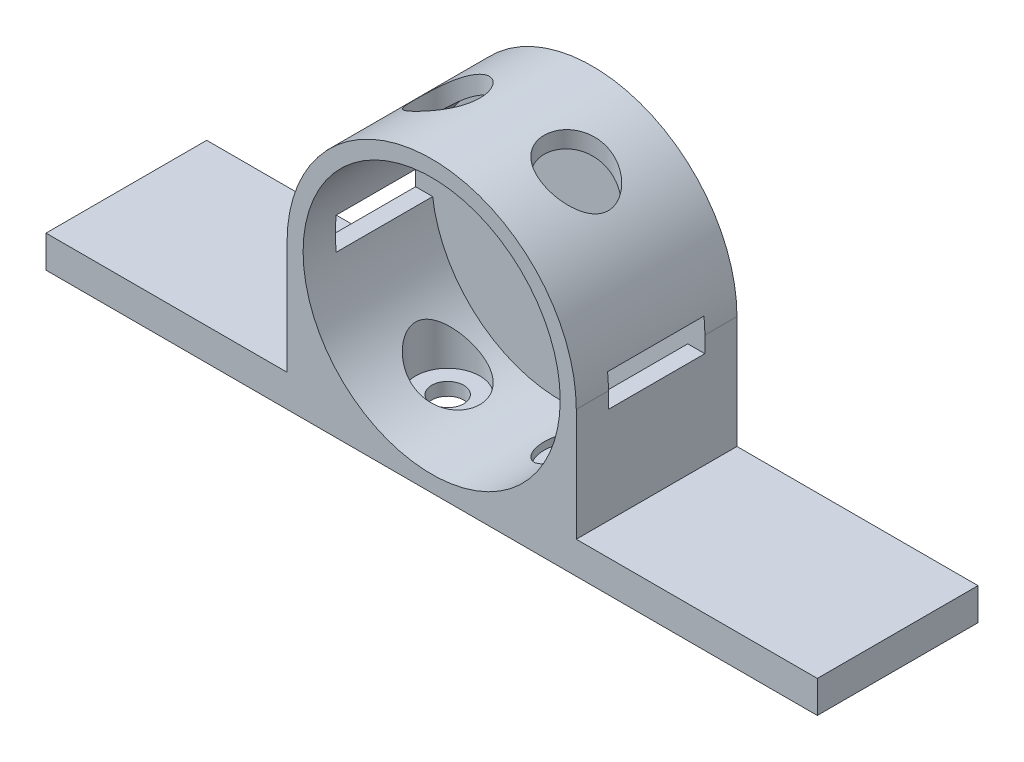
SolidWorks part; units mm, degrees
ref_plane "Front Plane" through (0, 0, 0) normal (0, 0, 1) x (1, 0, 0)
ref_plane "Top Plane" through (0, 0, 0) normal (0, 1, 0) x (1, 0, 0)
ref_plane "Right Plane" through (0, 0, 0) normal (1, 0, 0) x (0, 0, -1)
sketch "Sketch2" plane through (0, 0, 0) normal (0, 0, 1) x (1, 0, 0)
  circle A1 centre (0, 0) radius 22.5
  dimension "D2" = 45
extrude "Boss-Extrude3" add sketch "Sketch2" along normal blind 25
sketch "Sketch6" plane through (0, 0, 0) normal (0, 0, 1) x (1, 0, 0)
  line L1 (-22.5, 0) -> (22.5, 0)
  line L2 (-22.5, 0) -> (-22.5, -22.5)
  line L3 (-22.5, -22.5) -> (22.5, -22.5)
  line L4 (22.5, 0) -> (22.5, -22.5)
  circle A0 centre (0, 0) radius 22.5 construction
extrude "Boss-Extrude4" add sketch "Sketch6" along normal blind 25
sketch "Sketch4" plane through (0, 0, 25) normal (0, 0, 1) x (1, 0, 0)
  circle A0 centre (0, 0) radius 20
  dimension "D1" = 40
extrude "Cut-Extrude1" cut sketch "Sketch4" against normal blind 20
sketch "Sketch5" plane through (0, 0, 0) normal (0, 0, -1) x (-1, 0, 0)
  circle A0 centre (0, 0) radius 2.5
  dimension "D1" = 5
extrude "Cut-Extrude2" cut sketch "Sketch5" against normal up to surface (5 mm away) up to face at (20, 0, 5)
sketch "Sketch7" plane through (0, -22.5, 0) normal (0, -1, 0) x (1, 0, 0)
  line L0 (0, 25) -> (0, 0) construction
  line L1 (-22.5, 25) -> (22.5, 25) construction
  circle A3 centre (-10, 12.5) radius 5
  circle A4 centre (10, 12.5) radius 5
  point P9 (0, 12.5)
  dimension "D2" = 10
  dimension "D4" = 10
extrude "Cut-Extrude6" cut sketch "Sketch7" against normal through all
sketch "Sketch9" plane through (0, -22.5, 0) normal (0, -1, 0) x (1, 0, 0)
  line L0 (0, 25) -> (0, 0) construction
  line L1 (-22.5, 25) -> (22.5, 25) construction
  circle A0 centre (-10, 12.5) radius 5
  circle A1 centre (-10, 12.5) radius 2.5
  circle A2 centre (10, 12.5) radius 2.5
  circle A3 centre (10, 12.5) radius 5
  dimension "D1" = 10
  dimension "D2" = 5
extrude "Boss-Extrude5" add sketch "Sketch9" against normal blind 2
sketch "Sketch14" plane through (22.5, 0, 0) normal (1, 0, 0) x (0, 0, -1)
  line L0 (-25, 0) -> (0, 0) construction
  line L1 (-20, 0) -> (-5, 0)
  line L2 (-20, 2.5) -> (-20, -2.5)
  line L3 (-20, -2.5) -> (-5, -2.5)
  line L4 (-5, 2.5) -> (-5, -2.5)
  line L5 (0, -22.5) -> (0, 0) construction
  line L6 (-25, -22.5) -> (-25, 0) construction
  line L7 (-20, 2.5) -> (-5, 2.5)
  dimension "D1" = 5
  dimension "D2" = 5
  dimension "D3" = 2.5
extrude "Cut-Extrude8" cut sketch "Sketch14" against normal through all contours L7 L4 L3 L2
sketch "Sketch15" plane through (-22.5, 0, 0) normal (-1, 0, 0) x (0, 0, 1)
  line L0 (25, 0) -> (25, -22.5) construction
  line L1 (0, -22.5) -> (25, -22.5)
  line L2 (0, -22.5) -> (0, -17.5)
  line L3 (0, -17.5) -> (25, -17.5)
  line L4 (25, -22.5) -> (25, -17.5)
  dimension "D1" = 5
extrude "Boss-Extrude6" add sketch "Sketch15" along normal blind 37.5
sketch "Sketch16" plane through (22.5, 0, 0) normal (1, 0, 0) x (0, 0, -1)
  line L0 (0, -22.5) -> (0, 0) construction
  line L1 (-25, -22.5) -> (0, -22.5)
  line L2 (-25, -22.5) -> (-25, -17.5)
  line L3 (-25, -17.5) -> (0, -17.5)
  line L4 (0, -22.5) -> (0, -17.5)
  dimension "D1" = 5
extrude "Boss-Extrude7" add sketch "Sketch16" along normal blind 37.5
